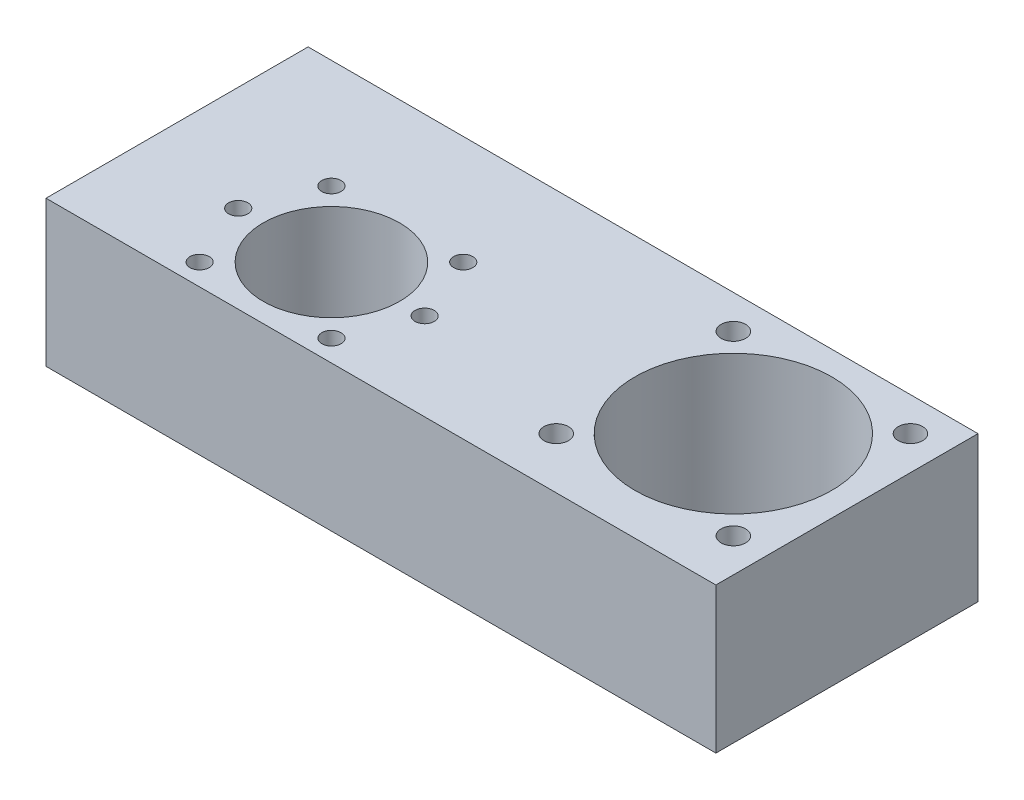
SolidWorks part; units mm, degrees
ref_plane "Front Plane" through (0, 0, 0) normal (0, 0, 1) x (1, 0, 0)
ref_plane "Top Plane" through (0, 0, 0) normal (0, 1, 0) x (1, 0, 0)
ref_plane "Right Plane" through (0, 0, 0) normal (1, 0, 0) x (0, 0, -1)
sketch "Sketch1" plane through (0, 0, 0) normal (0, 1, 0) x (1, 0, 0)
  line L1 (0, 0) -> (-115, 0)
  line L2 (0, 0) -> (0, 45)
  line L3 (0, 45) -> (-115, 45)
  line L4 (-115, 0) -> (-115, 45)
  dimension "D1" = 45
  dimension "D2" = 115
extrude "Boss-Extrude1" add sketch "Sketch1" along normal blind 25 contours L1 L4 L3 L2
sketch "Sketch2" plane through (0, 0, 0) normal (0, -1, 0) x (1, 0, 0)
  circle A0 centre (-81, -15) radius 10.7 construction
  circle A1 centre (-21, -24) radius 15.9 construction
  circle A2 centre (-81, -15) radius 10.7 construction
  circle A3 centre (-21, -24) radius 15.9 construction
  circle A4 centre (-81, -15) radius 11.7
  circle A5 centre (-21, -24) radius 16.9
  dimension "D1" = 1
extrude "Cut-Extrude1" cut sketch "Sketch2" against normal through all
sketch "Sketch3" plane through (0, 0, 0) normal (0, -1, 0) x (1, 0, 0)
  circle A0 centre (-69.6863, -3.6863) radius 2.35 construction
  circle A1 centre (-69.6863, -3.6863) radius 2.35 construction
  circle A2 centre (-65, -15) radius 2.35 construction
  circle A3 centre (-65, -15) radius 2.35 construction
  circle A4 centre (-69.6863, -26.3137) radius 2.35 construction
  circle A5 centre (-69.6863, -26.3137) radius 2.35 construction
  circle A6 centre (-92.3137, -26.3137) radius 2.35 construction
  circle A7 centre (-92.3137, -26.3137) radius 2.35 construction
  circle A8 centre (-97, -15) radius 2.35 construction
  circle A9 centre (-97, -15) radius 2.35 construction
  circle A10 centre (-92.3137, -3.6863) radius 2.35 construction
  circle A11 centre (-92.3137, -3.6863) radius 2.35 construction
  circle A12 centre (-5.7972, -8.7972) radius 2.75 construction
  circle A13 centre (-5.7972, -39.2028) radius 2.75 construction
  circle A14 centre (-36.2028, -39.2028) radius 2.75 construction
  circle A15 centre (-36.2028, -8.7972) radius 2.75 construction
  circle A16 centre (-69.6863, -3.6863) radius 2.35
  circle A17 centre (-69.6863, -3.6863) radius 2.35
  circle A18 centre (-65, -15) radius 2.35
  circle A19 centre (-65, -15) radius 2.35
  circle A20 centre (-69.6863, -26.3137) radius 2.35
  circle A21 centre (-69.6863, -26.3137) radius 2.35
  circle A22 centre (-92.3137, -26.3137) radius 2.35
  circle A23 centre (-92.3137, -26.3137) radius 2.35
  circle A24 centre (-97, -15) radius 2.35
  circle A25 centre (-97, -15) radius 2.35
  circle A26 centre (-92.3137, -3.6863) radius 2.35
  circle A27 centre (-92.3137, -3.6863) radius 2.35
  circle A28 centre (-5.7972, -8.7972) radius 2.75
  circle A29 centre (-5.7972, -39.2028) radius 2.75
  circle A30 centre (-36.2028, -39.2028) radius 2.75
  circle A31 centre (-36.2028, -8.7972) radius 2.75
hole_wizard "M5x0.8 Tapped Hole1" positions "Sketch4" profile "Sketch5" tap size "M5x0.8" standard "ANSI Metric" end condition through all
sketch "Sketch4" plane through (0, 0, 0) normal (0, -1, 0) x (-1, 0, 0)
  point P0 (36.2028, 39.2028)
  point P3 (5.7972, 39.2028)
  point P6 (5.7972, 8.7972)
  point P9 (36.2028, 8.7972)
sketch "Sketch5" plane through (-36.2028, 0, -39.2028) normal (1, 0, 0) x (0, 0, -1)
  line L0 (0, 0) -> (0, 25)
  line L1 (0, 25) -> (2.1, 25)
  line L2 (2.1, 25) -> (2.1, 0)
  line L5 (2.1, 0) -> (0, 0)
  line L11 (0, -6.35) -> (0, 107.95) construction
  dimension "Thru Tap Drill Dia." = 4.2
  dimension "Thru Tap Drill Depth" = 25
cosmetic thread "Hole Thread1"
cosmetic thread "Hole Thread2"
cosmetic thread "Hole Thread3"
cosmetic thread "Hole Thread4"
hole_wizard "M4x0.7 Tapped Hole1" positions "Sketch6" profile "Sketch7" tap size "M4x0.7" standard "ANSI Metric" end condition through all
sketch "Sketch6" plane through (0, 0, 0) normal (0, -1, 0) x (-1, 0, 0)
  point P0 (92.3137, 3.6863)
  point P3 (97, 15)
  point P6 (92.3137, 26.3137)
  point P9 (69.6863, 26.3137)
  point P12 (65, 15)
  point P15 (69.6863, 3.6863)
sketch "Sketch7" plane through (-92.3137, 0, -3.6863) normal (1, 0, 0) x (0, 0, -1)
  line L0 (0, 0) -> (0, 25)
  line L1 (0, 25) -> (1.65, 25)
  line L2 (1.65, 25) -> (1.65, 0)
  line L5 (1.65, 0) -> (0, 0)
  line L11 (0, -6.35) -> (0, 107.95) construction
  dimension "Thru Tap Drill Dia." = 3.3
  dimension "Thru Tap Drill Depth" = 25
cosmetic thread "Hole Thread5"
cosmetic thread "Hole Thread6"
cosmetic thread "Hole Thread7"
cosmetic thread "Hole Thread8"
cosmetic thread "Hole Thread9"
cosmetic thread "Hole Thread10"
